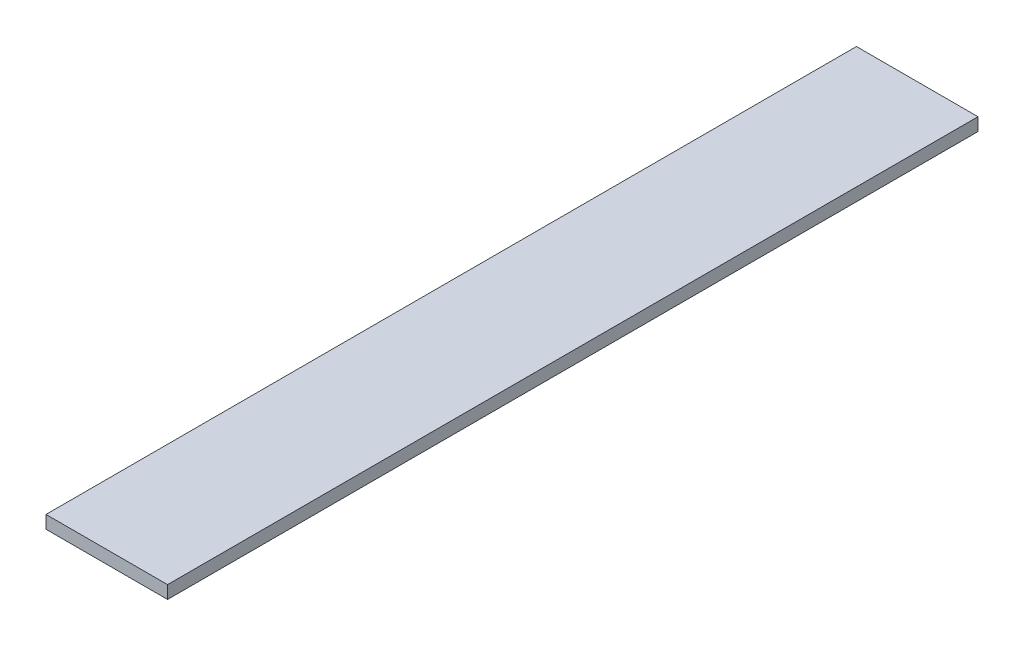
SolidWorks part; units mm, degrees
ref_plane "Front Plane" through (0, 0, 0) normal (0, 0, 1) x (1, 0, 0)
ref_plane "Top Plane" through (0, 0, 0) normal (0, 1, 0) x (1, 0, 0)
ref_plane "Right Plane" through (0, 0, 0) normal (1, 0, 0) x (0, 0, -1)
sketch "Sketch1" plane through (0, 0, 0) normal (0, 1, 0) x (1, 0, 0)
  line L1 (0, 0) -> (30, 0)
  line L2 (0, 0) -> (0, 200)
  line L3 (0, 200) -> (30, 200)
  line L4 (30, 0) -> (30, 200)
  dimension "D1" = 30
  dimension "D2" = 200
extrude "Boss-Extrude1" add sketch "Sketch1" along normal blind 3.175
